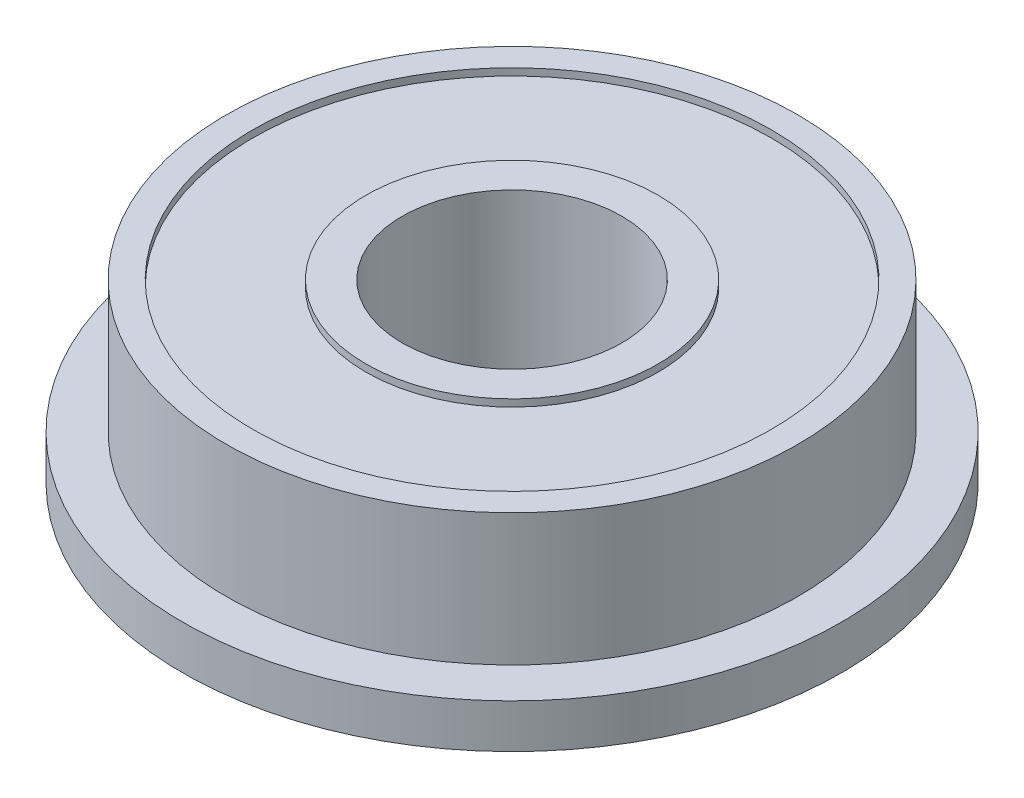
SolidWorks part; units mm, degrees
ref_plane "Front Plane" through (0, 0, 0) normal (0, 0, 1) x (1, 0, 0)
ref_plane "Top Plane" through (0, 0, 0) normal (0, 1, 0) x (1, 0, 0)
ref_plane "Right Plane" through (0, 0, 0) normal (1, 0, 0) x (0, 0, -1)
sketch "Sketch1" plane through (0, 0, 0) normal (0, 0, 1) x (1, 0, 0)
  line L0 (0, 0) -> (0, 8.0745) construction
  line L1 (2.5, 0) -> (3.3262, 0)
  line L2 (7.5, 0) -> (7.5, 1)
  line L3 (7.5, 1) -> (6.5, 1)
  line L4 (6.5, 1) -> (6.5, 4)
  line L5 (6.5, 4) -> (5.9036, 4)
  line L6 (2.5, 4) -> (2.5, 0)
  line L7 (3.3262, 4) -> (3.3262, 3.8378)
  line L8 (3.3262, 3.8378) -> (5.9036, 3.8378)
  line L9 (5.9036, 3.8378) -> (5.9036, 4)
  line L10 (2.5, 2) -> (4.0559, 2) construction
  line L11 (5.9036, 0.1622) -> (5.9036, 0)
  line L12 (3.3262, 0.1622) -> (5.9036, 0.1622)
  line L13 (3.3262, 0) -> (3.3262, 0.1622)
  line L14 (3.3262, 4) -> (2.5, 4)
  line L15 (5.9036, 0) -> (7.5, 0)
  dimension "D1" = 1
  dimension "D2" = 3
  dimension "D3" = 5
  dimension "D4" = 13
  dimension "D5" = 15
revolve "Revolve1" add sketch "Sketch1" angle 360 about L0
